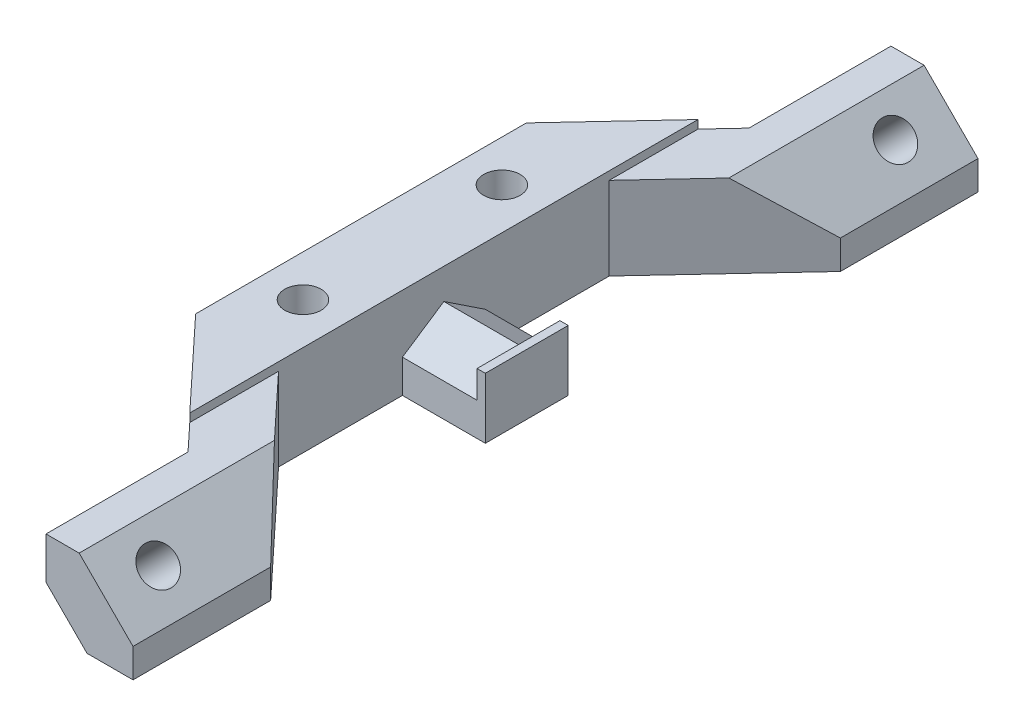
SolidWorks part; units mm, degrees
ref_plane "Front Plane" through (0, 0, 0) normal (0, 0, 1) x (1, 0, 0)
ref_plane "Top Plane" through (0, 0, 0) normal (0, 1, 0) x (1, 0, 0)
ref_plane "Right Plane" through (0, 0, 0) normal (1, 0, 0) x (0, 0, -1)
sketch "Sketch1" plane through (0, 0, 0) normal (0, 1, 0) x (1, 0, 0)
  line L0 (-5, 19.95) -> (7.9685, 33.8359)
  line L2 (-5, -19.95) -> (-5, 19.95)
  line L4 (5, -19.95) -> (5, 19.95)
  line L5 (-5, -19.95) -> (5, 19.95) construction
  line L6 (-5, 19.95) -> (5, -19.95) construction
  line L7 (5, 19.95) -> (18.4685, 34.3713)
  line L8 (18.4685, 34.3713) -> (18.4685, 50.9713)
  line L9 (18.4685, 50.9713) -> (7.9685, 50.9713)
  line L10 (7.9685, 50.9713) -> (7.9685, 33.8359)
  line L11 (0, 0) -> (30.4293, 0) construction
  line L12 (5, -19.95) -> (18.4685, -34.3713)
  line L13 (-5, -19.95) -> (7.9685, -33.8359)
  line L14 (7.9685, -50.9713) -> (7.9685, -33.8359)
  line L15 (18.4685, -50.9713) -> (7.9685, -50.9713)
  line L16 (18.4685, -34.3713) -> (18.4685, -50.9713)
  point P0 (0, 0)
  dimension "D1" = 10
  dimension "D2" = 39.9
  dimension "D3" = 16.6
  dimension "D4" = 10.5
  dimension "D5" = 19
  dimension "D6" = 23.4685
extrude "Boss-Extrude1" add sketch "Sketch1" along normal blind 10
sketch "Sketch2" plane through (0, 0, 50.9713) normal (0, 0, 1) x (1, 0, 0)
  line L0 (18.4685, 0) -> (18.4685, 3.5)
  line L1 (18.4685, 10) -> (18.4685, 0) construction
  line L2 (18.4685, 3.5) -> (11.9685, 10)
  line L3 (7.9685, 10) -> (18.4685, 10) construction
  line L4 (11.9685, 10) -> (7.9685, 10)
  line L14 (18.4685, 3.5) -> (18.4685, 10)
  line L15 (18.4685, 10) -> (11.9685, 10)
  dimension "D1" = 4
  dimension "D2" = 3.5
  dimension "D3" = 225
extrude "Cut-Extrude1" cut sketch "Sketch2" along direction (0, 0, -1) on the side against the normal through all contours L2 M2 M3
sketch "Sketch4" plane through (0, 0, 50.9713) normal (0, 0, 1) x (1, 0, 0)
  line L0 (7.9685, 4.9497) -> (7.9685, 0)
  line L1 (18.4685, 3.5) -> (11.9685, 10) construction
  line L2 (7.9685, 10) -> (7.9685, 0) construction
  line L3 (7.9685, 4.9497) -> (12.9182, 0)
  line L4 (7.9685, 0) -> (18.4685, 0) construction
  line L8 (7.9685, 0) -> (12.9182, 0)
  dimension "D1" = 7
sketch "Sketch13" plane through (5, 0, 0) normal (1, 0, 0) x (0, 0, -1)
  line L0 (0, 0) -> (0, 7.3166) construction
  line L3 (-19.95, 0) -> (19.95, 0) construction
  line L5 (0, 7.3166) -> (-5, 4)
  line L6 (-5, 4) -> (-5, 0)
  line L7 (-5, 0) -> (5, 0)
  line L9 (5, 4) -> (5, 0)
  line L10 (0, 7.3166) -> (5, 4)
  point P11 (0, 0)
  dimension "D1" = 4
  dimension "D2" = 6
  dimension "D3" = 5
sketch "Sketch15" plane through (10.9842, 10.9843, 0) normal (0.7071, 0.7071, 0) x (0, 0, -1)
  line L0 (50.9713, -10.5843) -> (50.9713, -1.3919) construction
  line L2 (0, 0) -> (0, 36.1783) construction
  line L3 (50.9713, -10.5843) -> (34.3713, -10.5843) construction
  circle A0 centre (44.4713, -5.6853) radius 2.2
  circle A1 centre (-44.4713, -5.6853) radius 2.2
  dimension "D2" = 4.4
  dimension "D1" = 6.5
  dimension "D3" = 4.899
extrude "Cut-Extrude5" cut sketch "Sketch15" against normal through all
sketch "Sketch17" plane through (0, 10, 0) normal (0, 1, 0) x (1, 0, 0)
  line L0 (0, 12) -> (0, 0) construction
  line L1 (0, 0) -> (0, -12) construction
  line L2 (5, -19.95) -> (5, 19.95) construction
  circle A0 centre (0, 12) radius 2.2
  circle A1 centre (0, -12) radius 2.2
  dimension "D1" = 4.4
  dimension "D2" = 24
  dimension "D3" = 5
extrude "Cut-Extrude6" cut sketch "Sketch4" against normal blind 15
sketch "Sketch18" plane through (0, 0, -50.9713) normal (0, 0, -1) x (-1, 0, 0)
  line L0 (-7.9685, 5) -> (-7.9685, 0)
  line L1 (-7.9685, 10) -> (-7.9685, 0) construction
  line L2 (-7.9685, 5) -> (-12.9182, 0)
  line L3 (-12.9182, 0) -> (-7.9685, 0)
extrude "Cut-Extrude7" cut sketch "Sketch18" against normal blind 15
extrude "Boss-Extrude2" add sketch "Sketch13" along normal blind 9
sketch "Sketch21" plane through (14, 0, 0) normal (1, 0, 0) x (0, 0, -1)
  line L0 (-5, 0) -> (5, 0)
  line L1 (5, 0) -> (5, 7.3166)
  line L2 (5, 7.3166) -> (-5, 7.3166)
  line L3 (-5, 7.3166) -> (-5, 0)
extrude "Boss-Extrude3" add sketch "Sketch21" along normal blind 1
extrude "Cut-Extrude8" cut sketch "Sketch17" against normal through all
sketch "Sketch22" plane through (0, 0, 0) normal (0, -1, 0) x (1, 0, 0)
  circle A0 centre (0, 12) radius 3.5
  circle A1 centre (0, -12) radius 3.5
  dimension "D1" = 7
extrude "Cut-Extrude9" cut sketch "Sketch22" against normal blind 4
sketch "Sketch23" plane through (0, 10, 0) normal (0, 1, 0) x (1, 0, 0)
  line L0 (5, -30.6574) -> (5, 30.6574)
  line L1 (-5, -19.95) -> (7.9685, -33.8359) construction
  line L2 (7.9685, 33.8359) -> (-5, 19.95) construction
  line L3 (5, 30.6574) -> (-5, 19.95)
  line L4 (-5, 19.95) -> (-5, -19.95)
  line L5 (-5, -19.95) -> (5, -30.6574)
  circle A0 centre (0, -12) radius 2.2
  circle A1 centre (0, 12) radius 2.2
  dimension "D1" = 4.4
extrude "Boss-Extrude4" add sketch "Sketch23" along normal blind 1
